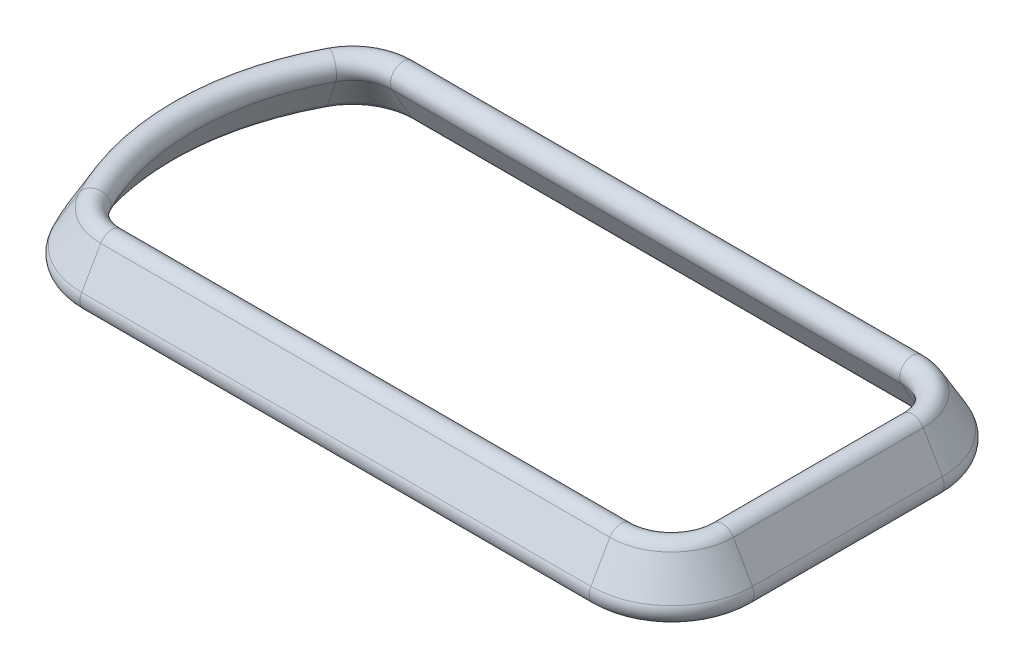
SolidWorks part; units mm, degrees
ref_plane "Vorne" through (0, 0, 0) normal (0, 0, 1) x (1, 0, 0)
ref_plane "Oben" through (0, 0, 0) normal (0, 1, 0) x (1, 0, 0)
ref_plane "Rechts" through (0, 0, 0) normal (1, 0, 0) x (0, 0, -1)
sketch "Skizze1" plane through (0, 0, 0) normal (0, 1, 0) x (1, 0, 0)
  line L1 (-100.351, -57.4328) -> (100.351, -57.4328)
  line L3 (-100.351, 57.4328) -> (100.351, 57.4328)
  line L4 (120.351, -37.4328) -> (120.351, 37.4328)
  line L5 (0, 57.4328) -> (0, -57.4328) construction
  line L6 (-107.3009, 0) -> (120.351, 0) construction
  arc A0 (-100.351, -57.4328) -> (-118.0266, -46.791) centre (-100.351, -37.4328) cw
  arc A1 (100.351, 57.4328) -> (120.351, 37.4328) centre (100.351, 37.4328) cw
  arc A2 (100.351, -57.4328) -> (120.351, -37.4328) centre (100.351, -37.4328) ccw
  arc A3 (-118.0266, 46.791) -> (-100.351, 57.4328) centre (-100.351, 37.4328) cw
  arc A4 (-118.0266, -46.791) -> (-118.0266, 46.791) centre (-29.649, 0) cw
  point P0 (0, 0)
  dimension "D1" = 20
  dimension "D2" = 100
  dimension "D3" = 114.8656
  dimension "D4" = 150
sketch "Skizze2" plane through (0, 0, 0) normal (0, 0, 1) x (1, 0, 0)
  line L2 (-129.649, 0) -> (-137.149, -12.9904) construction
  line L6 (-125.3188, -2.5) -> (-132.8188, -15.4904)
  line L7 (-133.9791, 2.5) -> (-141.4791, -10.4904)
  line L10 (-107.3009, 0) -> (120.351, 0) construction
  arc A0 (-125.3188, -2.5) -> (-133.9791, 2.5) centre (-129.649, 0) ccw
  arc A1 (-141.4791, -10.4904) -> (-132.8188, -15.4904) centre (-137.149, -12.9904) ccw
  point P2 (-133.399, -6.4952)
  dimension "D2" = 5
  dimension "D1" = 120
  dimension "D3" = 15
sweep "Austragung2" add profiles "Skizze2" path "Skizze1"
